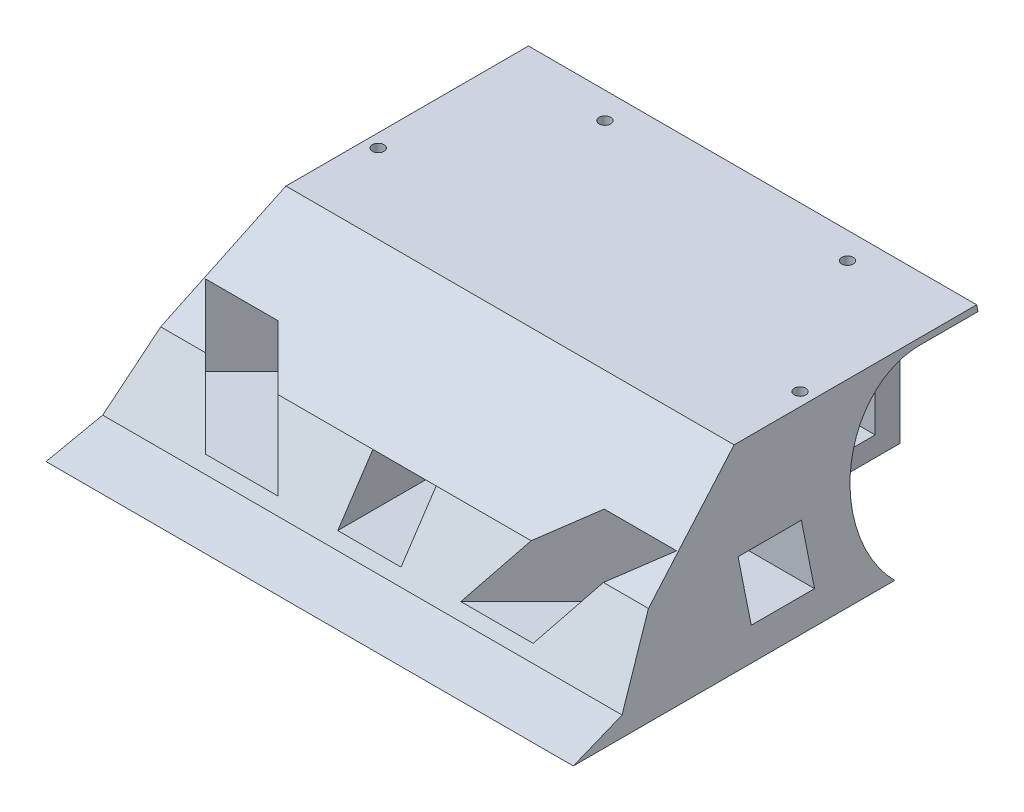
SolidWorks part; units mm, degrees
ref_plane "Ön Düzlem" through (0, 0, 0) normal (0, 0, 1) x (1, 0, 0)
ref_plane "Üst Düzlem" through (0, 0, 0) normal (0, 1, 0) x (1, 0, 0)
ref_plane "Sağ Düzlem" through (0, 0, 0) normal (1, 0, 0) x (0, 0, -1)
sketch "Çizim2" plane through (0, 0, 0) normal (0, 1, 0) x (1, 0, 0)
  line L1 (-55.3298, 53.196) -> (44.6702, 53.196)
  line L2 (-55.3298, 53.196) -> (-55.3298, -36.804)
  line L3 (-55.3298, -36.804) -> (44.6702, -36.804)
  line L4 (44.6702, 53.196) -> (44.6702, -36.804)
  dimension "D1" = 90
  dimension "D2" = 100
extrude "Yükseklik-Ekstrüzyon1" add sketch "Çizim2" along normal blind 30
sketch "Çizim5" plane through (44.6702, 0, 0) normal (1, 0, 0) x (0, 0, -1)
  line L0 (53.196, 30) -> (53.196, 0) construction
  line L1 (-36.804, 30) -> (53.196, 30) construction
  line L2 (36.196, 29) -> (53.196, 29)
  line L3 (53.196, 29) -> (53.196, 0)
  line L4 (53.196, 0) -> (24.1544, 0)
  arc A0 (36.196, 29) -> (24.1544, 0) centre (36.196, 12) ccw
  dimension "D2" = 34
  dimension "D1" = 17
  dimension "D3" = 18
extrude "Kes-Ekstrüzyon11" cut sketch "Çizim5" against normal blind 22
sketch "Çizim6" plane through (-55.3298, 0, 0) normal (-1, 0, 0) x (0, 0, 1)
  line L0 (-53.196, 30) -> (36.804, 30) construction
  line L1 (-53.196, 30) -> (-53.196, 0) construction
  line L2 (-36.196, 29) -> (-53.196, 29)
  line L3 (-53.196, 29) -> (-53.196, 0)
  line L4 (-53.196, 0) -> (-24.1544, 0)
  arc A0 (-24.1544, 0) -> (-36.196, 29) centre (-36.196, 12) ccw
  dimension "D1" = 34
  dimension "D2" = 18
  dimension "D3" = 17
extrude "Kes-Ekstrüzyon12" cut sketch "Çizim6" against normal blind 22
sketch "Çizim7" plane through (22.6702, 0, 0) normal (1, 0, 0) x (0, 0, -1)
  line L0 (53.196, 0) -> (53.196, 29) construction
  line L1 (29.946, 20.25) -> (42.446, 20.25)
  line L2 (29.946, 20.25) -> (29.946, 3.75)
  line L3 (29.946, 3.75) -> (42.446, 3.75)
  line L4 (42.446, 20.25) -> (42.446, 3.75)
  line L5 (-36.804, 30) -> (53.196, 30) construction
  dimension "D1" = 12.5
  dimension "D2" = 16.5
  dimension "D3" = 10.75
  dimension "D4" = 9.75
extrude "Kes-Ekstrüzyon13" cut sketch "Çizim7" against normal blind 70
sketch "Çizim8" plane through (22.6702, 0, 0) normal (1, 0, 0) x (0, 0, -1)
  line L0 (-36.804, 30) -> (53.196, 30) construction
  line L1 (53.196, 0) -> (47.196, 0)
  line L2 (53.196, 0) -> (53.196, 30)
  line L3 (53.196, 30) -> (47.196, 30)
  line L4 (47.196, 0) -> (47.196, 30)
  dimension "D1" = 6
extrude "Kes-Ekstrüzyon14" cut sketch "Çizim8" against normal blind 100
sketch "Çizim9" plane through (0, 30, 0) normal (0, 1, 0) x (1, 0, 0)
  line L1 (22.6702, 47.196) -> (44.6702, 47.196)
  line L2 (22.6702, 47.196) -> (22.6702, 53.196)
  line L3 (22.6702, 53.196) -> (44.6702, 53.196)
  line L4 (44.6702, 47.196) -> (44.6702, 53.196)
extrude "Kes-Ekstrüzyon15" cut sketch "Çizim9" against normal blind 100
sketch "Çizim10" plane through (44.6702, 0, 0) normal (1, 0, 0) x (0, 0, -1)
  line L0 (-36.804, 0) -> (24.1544, 0) construction
  line L1 (10.196, 15) -> (-1.804, 15)
  line L2 (10.196, 15) -> (10.196, 5)
  line L3 (10.196, 5) -> (-1.804, 5)
  line L4 (-1.804, 15) -> (-1.804, 5)
  dimension "D1" = 12
  dimension "D2" = 5
  dimension "D4" = 10
extrude "Kes-Ekstrüzyon16" cut sketch "Çizim10" against normal blind 100
sketch "Çizim11" plane through (0, 0, 36.804) normal (0, 0, 1) x (1, 0, 0)
  line L0 (-55.3298, 0) -> (44.6702, 0) construction
  line L1 (-11.3298, 15) -> (0.6702, 15)
  line L2 (-11.3298, 15) -> (-11.3298, 5)
  line L3 (-11.3298, 5) -> (0.6702, 5)
  line L4 (0.6702, 15) -> (0.6702, 5)
  dimension "D1" = 5
  dimension "D2" = 12
  dimension "D3" = 10
  dimension "D4" = 44
extrude "Kes-Ekstrüzyon17" cut sketch "Çizim11" against normal blind 45
sketch "Çizim12" plane through (0, 30, 0) normal (0, 1, 0) x (1, 0, 0)
  line L0 (-11.3298, -36.804) -> (-17.2338, -42.708)
  line L1 (-17.2338, -42.708) -> (-17.2338, -36.804)
  line L2 (-55.3298, -36.804) -> (44.6702, -36.804) construction
  line L3 (-17.2338, -36.804) -> (-11.3298, -36.804)
  line L4 (0.6702, -36.804) -> (4.7185, -40.8523)
  line L5 (4.7185, -40.8523) -> (4.7185, -36.804)
  line L6 (4.7185, -36.804) -> (0.6702, -36.804)
extrude "Yükseklik-Ekstrüzyon2" add sketch "Çizim12" along normal blind 45 separate body
sketch "Çizim13" plane through (12.7371, 0, 12.7371) normal (0.7071, 0, 0.7071) x (0.7071, 0, -0.7071)
  line L0 (-31.9144, 5) -> (38.7962, 5) construction
  line L1 (-34.0358, 20.2) -> (-43.7358, 20.2)
  line L2 (-34.0358, 20.2) -> (-34.0358, 5)
  line L3 (-34.0358, 5) -> (-43.7358, 5)
  line L4 (-43.7358, 20.2) -> (-43.7358, 5)
  dimension "D1" = 9.7
  dimension "D2" = 15.2
  dimension "D3" = 0
extrude "Kes-Ekstrüzyon18" cut sketch "Çizim13" against normal blind 45
sketch "Çizim14" plane through (-18.0669, 0, 18.0669) normal (-0.7071, 0, 0.7071) x (0.7071, 0, 0.7071)
  line L1 (26.4983, 5) -> (36.1983, 5)
  line L2 (26.4983, 5) -> (26.4983, 20.2)
  line L3 (26.4983, 20.2) -> (36.1983, 20.2)
  line L4 (36.1983, 5) -> (36.1983, 20.2)
  dimension "D1" = 15.2
  dimension "D2" = 9.7
extrude "Kes-Ekstrüzyon19" cut sketch "Çizim14" against normal blind 45
sketch "Çizim15" plane through (0, 30, 0) normal (0, 1, 0) x (1, 0, 0)
  line L1 (-27.0077, -19.3241) -> (37.6405, -19.3241)
  line L2 (-27.0077, -19.3241) -> (-27.0077, -70.0426)
  line L3 (-27.0077, -70.0426) -> (37.6405, -70.0426)
  line L4 (37.6405, -19.3241) -> (37.6405, -70.0426)
extrude "Kes-Ekstrüzyon20" cut sketch "Çizim15" along normal blind 45
sketch "Çizim16" plane through (44.6702, 0, 0) normal (1, 0, 0) x (0, 0, -1)
  line L0 (-36.804, 0) -> (-26.804, 3)
  line L1 (-26.804, 3) -> (-18.804, 15)
  line L2 (-18.804, 15) -> (1.196, 30)
  line L3 (-36.804, 30) -> (47.196, 30) construction
  line L4 (1.196, 30) -> (-36.804, 30)
  line L5 (-36.804, 30) -> (-36.804, 0)
  line L6 (-36.804, 0) -> (24.1544, 0) construction
  point P11 (-26.4401, 5.6079)
  dimension "D1" = 10
  dimension "D2" = 3
  dimension "D3" = 8
  dimension "D4" = 20
  dimension "D5" = 12
extrude "Kes-Ekstrüzyon21" cut sketch "Çizim16" against normal blind 100
sketch "Çizim17" plane through (0, 30, 0) normal (0, 1, 0) x (1, 0, 0)
  line L0 (-55.3298, 47.196) -> (-55.3298, 1.196) construction
  line L1 (-55.3298, 47.196) -> (44.6702, 47.196) construction
  line L2 (-55.3298, 1.196) -> (44.6702, 1.196) construction
  line L3 (44.6702, 1.196) -> (44.6702, 47.196) construction
  circle A0 centre (-28.3298, 42.196) radius 1.1
  circle A1 centre (-45.3298, 16.196) radius 1.1
  circle A2 centre (34.6702, 16.196) radius 1.1
  circle A3 centre (17.6702, 42.196) radius 1.1
  dimension "D3" = 2.2
  dimension "D4" = 2.2
  dimension "D7" = 27
  dimension "D1" = 27
  dimension "D2" = 5
  dimension "D5" = 15
  dimension "D8" = 15
  dimension "D9" = 10
  dimension "D10" = 10
extrude "Kes-Ekstrüzyon24" cut sketch "Çizim17" against normal blind 100
sketch "Çizim19" plane through (0, 0, -47.196) normal (0, 0, -1) x (-1, 0, 0)
  line L0 (-44.6702, 0) -> (-37.1702, 30)
  line L1 (55.3298, 30) -> (-44.6702, 30) construction
  line L2 (-37.1702, 30) -> (-44.6702, 30)
  line L3 (-44.6702, 30) -> (-44.6702, 0)
  line L4 (55.3298, 0) -> (55.3298, 30)
  line L5 (55.3298, 30) -> (47.8298, 30)
  line L6 (47.8298, 30) -> (55.3298, 0)
  dimension "D1" = 7.5
  dimension "D2" = 7.5
extrude "Kes-Ekstrüzyon25" cut sketch "Çizim19" against normal blind 100
